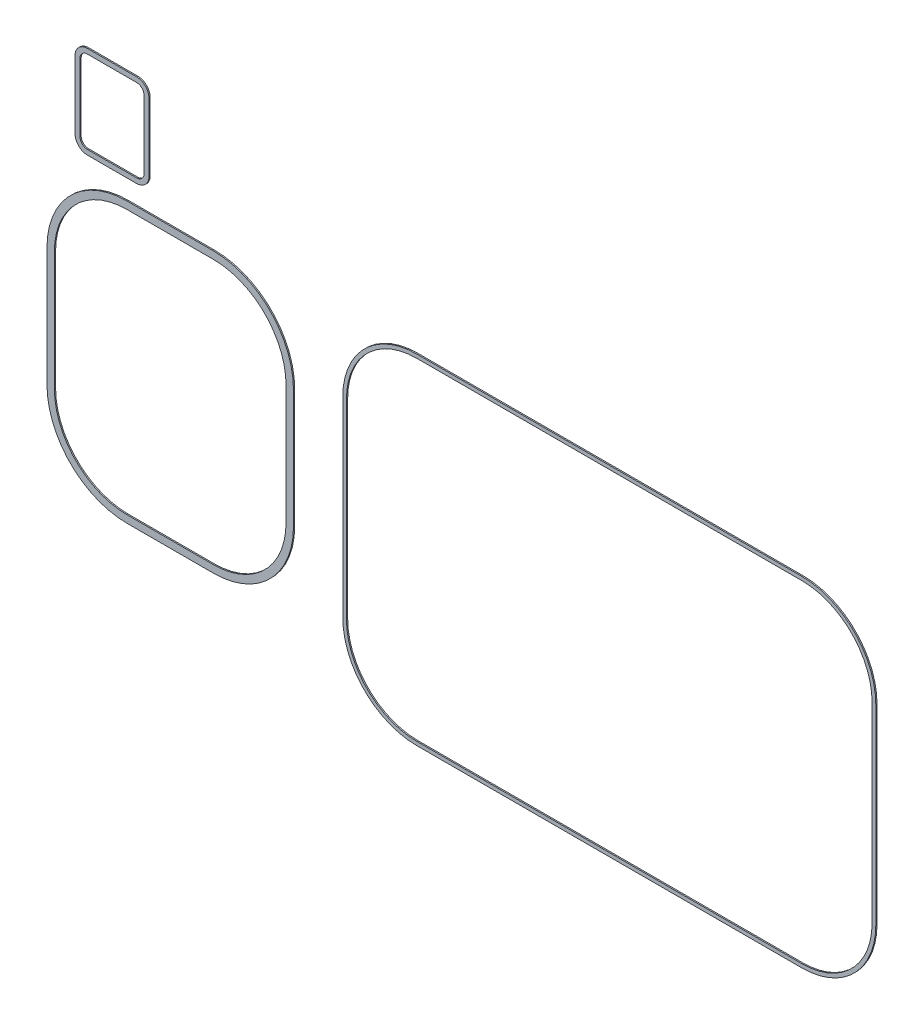
SolidWorks part; units mm, degrees
ref_plane "Front Plane" through (0, 0, 0) normal (0, 0, 1) x (1, 0, 0)
ref_plane "Top Plane" through (0, 0, 0) normal (0, 1, 0) x (1, 0, 0)
ref_plane "Right Plane" through (0, 0, 0) normal (1, 0, 0) x (0, 0, -1)
sketch "Sketch1" plane through (0, 0, 0) normal (0, 0, 1) x (1, 0, 0)
  line L0 (59707.0577, -1397.1064) -> (59707.0577, 5980.3737) construction
  line L1 (49145.0577, 46139.6336) -> (111645.0577, 46139.6336)
  line L2 (37145.0577, 34139.6336) -> (37145.0577, 3109.6336)
  line L3 (49145.0577, -8890.3664) -> (111645.0577, -8890.3664)
  line L4 (123645.0577, 34139.6336) -> (123645.0577, 3109.6336)
  line L5 (2145.0577, 44139.6336) -> (16145.0577, 44139.6336)
  line L6 (-10854.9423, 31139.6336) -> (-10854.9423, 11839.6336)
  line L7 (2145.0577, -1160.3664) -> (16145.0577, -1160.3664)
  line L8 (29145.0577, 31139.6336) -> (29145.0577, 11839.6336)
  line L9 (62943.8077, 2291.6336) -> (56470.3077, 2291.6336) construction
  line L10 (27945.0577, 31139.6336) -> (27945.0577, 11839.6336)
  line L11 (2145.0577, 39.6336) -> (16145.0577, 39.6336)
  line L12 (-9654.9423, 31139.6336) -> (-9654.9423, 11839.6336)
  line L13 (2145.0577, 42939.6336) -> (16145.0577, 42939.6336)
  line L14 (123045.0577, 34139.6336) -> (123045.0577, 3109.6336)
  line L15 (49145.0577, -8290.3664) -> (111645.0577, -8290.3664)
  line L16 (37745.0577, 34139.6336) -> (37745.0577, 3109.6336)
  line L17 (49145.0577, 45539.6336) -> (111645.0577, 45539.6336)
  line L18 (-8925.6397, 50753.328) -> (-8925.6397, 45347.7895) construction
  line L19 (3698.9995, 62369.7277) -> (-4301.0005, 62369.7277)
  line L20 (5698.9995, 60369.7277) -> (5698.9995, 49369.7277)
  line L21 (3698.9995, 47369.7277) -> (-4301.0005, 47369.7277)
  line L22 (-6301.0005, 60369.7277) -> (-6301.0005, 49369.7277)
  line L23 (-5501.0005, 60369.7277) -> (-5501.0005, 49369.7277)
  line L24 (3698.9995, 48169.7277) -> (-4301.0005, 48169.7277)
  line L25 (4898.9995, 60369.7277) -> (4898.9995, 49369.7277)
  line L26 (3698.9995, 61569.7277) -> (-4301.0005, 61569.7277)
  arc A0 (29145.0577, 31139.6336) -> (16145.0577, 44139.6336) centre (16145.0577, 31139.6336) ccw
  arc A1 (16145.0577, -1160.3664) -> (29145.0577, 11839.6336) centre (16145.0577, 11839.6336) ccw
  arc A2 (-10854.9423, 11839.6336) -> (2145.0577, -1160.3664) centre (2145.0577, 11839.6336) ccw
  arc A3 (2145.0577, 44139.6336) -> (-10854.9423, 31139.6336) centre (2145.0577, 31139.6336) ccw
  arc A4 (37145.0577, 34139.6336) -> (49145.0577, 46139.6336) centre (49145.0577, 34139.6336) cw
  arc A5 (49145.0577, -8890.3664) -> (37145.0577, 3109.6336) centre (49145.0577, 3109.6336) cw
  arc A6 (123645.0577, 3109.6336) -> (111645.0577, -8890.3664) centre (111645.0577, 3109.6336) cw
  arc A7 (111645.0577, 46139.6336) -> (123645.0577, 34139.6336) centre (111645.0577, 34139.6336) cw
  arc A8 (16145.0577, 39.6336) -> (27945.0577, 11839.6336) centre (16145.0577, 11839.6336) ccw
  arc A9 (-9654.9423, 11839.6336) -> (2145.0577, 39.6336) centre (2145.0577, 11839.6336) ccw
  arc A10 (2145.0577, 42939.6336) -> (-9654.9423, 31139.6336) centre (2145.0577, 31139.6336) ccw
  arc A11 (27945.0577, 31139.6336) -> (16145.0577, 42939.6336) centre (16145.0577, 31139.6336) ccw
  arc A12 (123045.0577, 3109.6336) -> (111645.0577, -8290.3664) centre (111645.0577, 3109.6336) cw
  arc A13 (49145.0577, -8290.3664) -> (37745.0577, 3109.6336) centre (49145.0577, 3109.6336) cw
  arc A14 (37745.0577, 34139.6336) -> (49145.0577, 45539.6336) centre (49145.0577, 34139.6336) cw
  arc A15 (111645.0577, 45539.6336) -> (123045.0577, 34139.6336) centre (111645.0577, 34139.6336) cw
  arc A16 (-6301.0005, 60369.7277) -> (-4301.0005, 62369.7277) centre (-4301.0005, 60369.7277) cw
  arc A17 (3698.9995, 62369.7277) -> (5698.9995, 60369.7277) centre (3698.9995, 60369.7277) cw
  arc A18 (5698.9995, 49369.7277) -> (3698.9995, 47369.7277) centre (3698.9995, 49369.7277) cw
  arc A19 (-6301.0005, 49369.7277) -> (-4301.0005, 47369.7277) centre (-4301.0005, 49369.7277) ccw
  arc A20 (-5501.0005, 49369.7277) -> (-4301.0005, 48169.7277) centre (-4301.0005, 49369.7277) ccw
  arc A21 (4898.9995, 49369.7277) -> (3698.9995, 48169.7277) centre (3698.9995, 49369.7277) cw
  arc A22 (3698.9995, 61569.7277) -> (4898.9995, 60369.7277) centre (3698.9995, 60369.7277) cw
  arc A23 (-5501.0005, 60369.7277) -> (-4301.0005, 61569.7277) centre (-4301.0005, 60369.7277) cw
  point P10 (29145.0577, 44139.6336)
  point P15 (-10854.9423, -1160.3664)
  point P18 (-10854.9423, 44139.6336)
  point P69 (-8925.6397, 49820.9024)
  dimension "D3" = 13000
  dimension "D4" = 12000
  dimension "D13" = 2000
  dimension "D14" = 2000
  dimension "D1" = 40000
  dimension "D2" = 45300
  dimension "D5" = 8000
  dimension "D6" = 86500
  dimension "D7" = 55030
  dimension "D8" = 63938
  dimension "D9" = 11182
  dimension "D10" = 2000
  dimension "D16" = 12000
  dimension "D17" = 15000
  dimension "D11" = 1200
  dimension "D12" = 600
  dimension "D15" = 800
extrude "Extrude1" add sketch "Sketch1" against normal up to surface (200 mm away)
